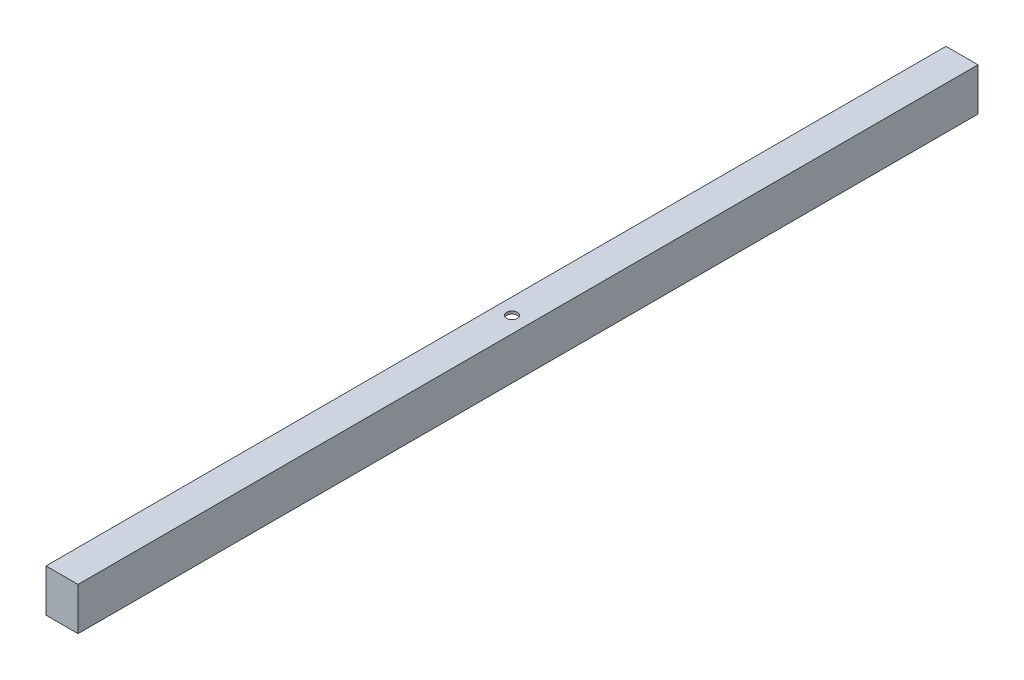
SolidWorks part; units mm, degrees
material "1023 Carbon Steel Sheet (SS)"
ref_plane "Front Plane" through (0, 0, 0) normal (0, 0, 1) x (1, 0, 0)
ref_plane "Top Plane" through (0, 0, 0) normal (0, 1, 0) x (1, 0, 0)
ref_plane "Right Plane" through (0, 0, 0) normal (1, 0, 0) x (0, 0, -1)
sketch "Sketch1" plane through (0, 0, 0) normal (0, 0, 1) x (1, 0, 0)
  line L1 (0, 0) -> (17.4625, 0)
  line L2 (0, 0) -> (0, 1.5875)
  line L3 (0, 1.5875) -> (19.05, 1.5875)
  line L4 (19.05, 0) -> (19.05, 1.5875)
  line L6 (19.05, 0) -> (19.05, -23.8125)
  line L7 (19.05, -23.8125) -> (12.7, -23.8125)
  line L8 (17.4625, 0) -> (17.4625, -22.225)
  line L9 (12.7, -23.8125) -> (0, -23.8125)
  line L11 (17.4625, -22.225) -> (0, -22.225)
  line L12 (0, -23.8125) -> (0, -22.225)
  dimension "D1" = 1.5875
  dimension "D2" = 1.5875
  dimension "D3" = 1.5875
  dimension "D4" = 25.4
  dimension "D5" = 19.05
extrude "Boss-Extrude1" add sketch "Sketch1" along normal blind 533.4 contours L1 L4 L3 L2 | L1 L8 L7 L6 | L12 L9 L8 L11
sketch "Sketch2" plane through (0, 1.5875, 0) normal (0, 1, 0) x (1, 0, 0)
  line L0 (0, 0) -> (19.05, 0) construction
  line L2 (19.05, -533.4) -> (19.05, 0) construction
  line L3 (19.05, -533.4) -> (19.05, 0)
  line L4 (19.05, -533.4) -> (0, -533.4)
  line L5 (9.525, -533.4) -> (9.525, -140.7524)
  circle A0 centre (9.525, -266.7) radius 3.175
  dimension "D1" = 6.35
  dimension "D3" = 9.525
  dimension "D2" = 266.7
extrude "Cut-Extrude1" cut sketch "Sketch2" against normal blind 381 contours A0
sketch "Sketch4" plane through (0, 0, 0) normal (0, 0, -1) x (-1, 0, 0)
  line L1 (-19.05, 1.5875) -> (0, 1.5875)
  line L2 (-19.05, 1.5875) -> (-19.05, -23.8125)
  line L3 (-19.05, -23.8125) -> (0, -23.8125)
  line L4 (0, 1.5875) -> (0, -23.8125)
extrude "Boss-Extrude3" add sketch "Sketch4" along normal blind 1.016
sketch "Sketch5" plane through (0, 0, 533.4) normal (0, 0, 1) x (1, 0, 0)
  line L1 (0, 1.5875) -> (19.05, 1.5875)
  line L2 (0, 1.5875) -> (0, -23.8125)
  line L3 (0, -23.8125) -> (19.05, -23.8125)
  line L4 (19.05, 1.5875) -> (19.05, -23.8125)
extrude "Boss-Extrude4" add sketch "Sketch5" along normal blind 1.016
